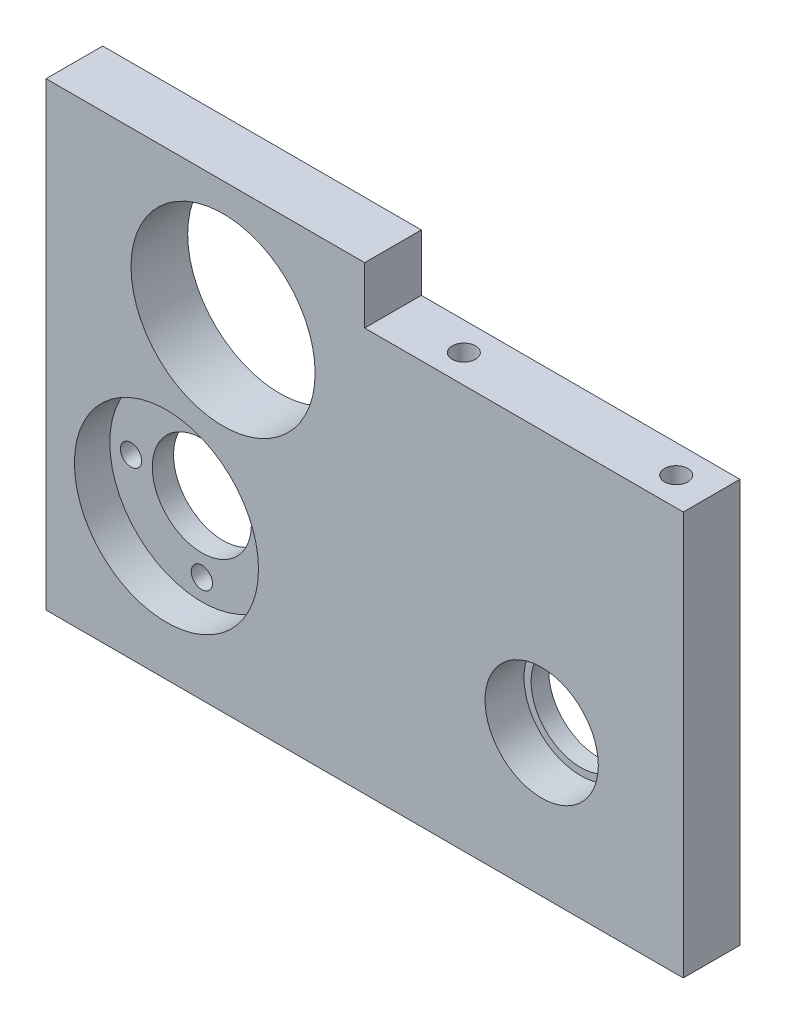
SolidWorks part; units mm, degrees
ref_plane "Front" through (0, 0, 0) normal (0, 0, 1) x (1, 0, 0)
ref_plane "Top" through (0, 0, 0) normal (0, 1, 0) x (1, 0, 0)
ref_plane "Right" through (0, 0, 0) normal (1, 0, 0) x (0, 0, -1)
sketch "Esquisse1" plane through (0, 0, 0) normal (0, 0, 1) x (1, 0, 0)
  line L1 (0, 0) -> (90, 0)
  line L2 (0, 0) -> (0, 65)
  line L3 (0, 65) -> (90, 65)
  line L4 (90, 0) -> (90, 65)
  circle A0 centre (70, 20) radius 7
  circle A1 centre (17, 20) radius 13
  circle A2 centre (25, 48) radius 13
  dimension "D3" = 14
  dimension "D4" = 20
  dimension "D6" = 53
  dimension "D8" = 26
  dimension "D9" = 26
  dimension "D1" = 90
  dimension "D2" = 65
  dimension "D5" = 70
  dimension "D7" = 20
  dimension "D10" = 53
  dimension "D11" = 48
extrude "Boss.-Extru.1" add sketch "Esquisse1" along normal blind 8
sketch "Esquisse2" plane through (0, 0, 0) normal (0, 0, -1) x (-1, 0, 0)
  circle A0 centre (-17, 20) radius 13
  circle A1 centre (-17, 20) radius 13 construction
extrude "Boss.-Extru.2" add sketch "Esquisse2" against normal blind 3
sketch "Esquisse3" plane through (0, 0, 3) normal (0, 0, 1) x (1, 0, 0)
  line L0 (27, 20) -> (17, 20) construction
  circle A0 centre (17, 20) radius 7
  circle A1 centre (27, 20) radius 1.5
  circle A2 centre (17, 10) radius 1.5
  circle A3 centre (7, 20) radius 1.5
  circle A4 centre (17, 30) radius 1.5
  point P13 (17, 20)
  dimension "D1" = 14
  dimension "D2" = 3
  dimension "D3" = 10
  dimension "D4" = 4
extrude "Enlèv. mat.-Extru.1" cut sketch "Esquisse3" against normal through all
sketch "Esquisse4" plane through (0, 0, 8) normal (0, 0, 1) x (1, 0, 0)
  circle A0 centre (70, 20) radius 8
  dimension "D1" = 16
extrude "Enlèv. mat.-Extru.2" cut sketch "Esquisse4" against normal blind 5.5
sketch "Esquisse5" plane through (0, 0, 8) normal (0, 0, 1) x (1, 0, 0)
  line L0 (90, 65) -> (0, 65) construction
  line L1 (45, 65) -> (90, 65)
  line L2 (45, 65) -> (45, 57)
  line L3 (45, 57) -> (90, 57)
  line L4 (90, 65) -> (90, 57)
  line L5 (90, 0) -> (90, 65) construction
  dimension "D1" = 8
  dimension "D2" = 45
extrude "Enlèv. mat.-Extru.3" cut sketch "Esquisse5" against normal through all
sketch "Esquisse6" plane through (0, 0, 0) normal (-1, 0, 0) x (0, 0, 1)
  line L0 (4, 0) -> (4, 65) construction
  line L1 (8, 0) -> (0, 0) construction
  line L2 (8, 65) -> (0, 65) construction
  circle A0 centre (4, 7) radius 1.65
  circle A1 centre (4, 45) radius 1.65
  dimension "D1" = 3.3
  dimension "D2" = 38
  dimension "D3" = 7
extrude "Enlèv. mat.-Extru.4" cut sketch "Esquisse6" against normal blind 10
sketch "Esquisse7" plane through (0, 57, 0) normal (0, 1, 0) x (1, 0, 0)
  line L0 (45, -4) -> (85, -4) construction
  line L1 (45, 0) -> (45, -8) construction
  circle A0 centre (85, -4) radius 1.65
  circle A1 centre (55, -4) radius 1.65
  dimension "D1" = 3.3
  dimension "D2" = 30
  dimension "D3" = 10
extrude "Enlèv. mat.-Extru.5" cut sketch "Esquisse7" against normal blind 10
